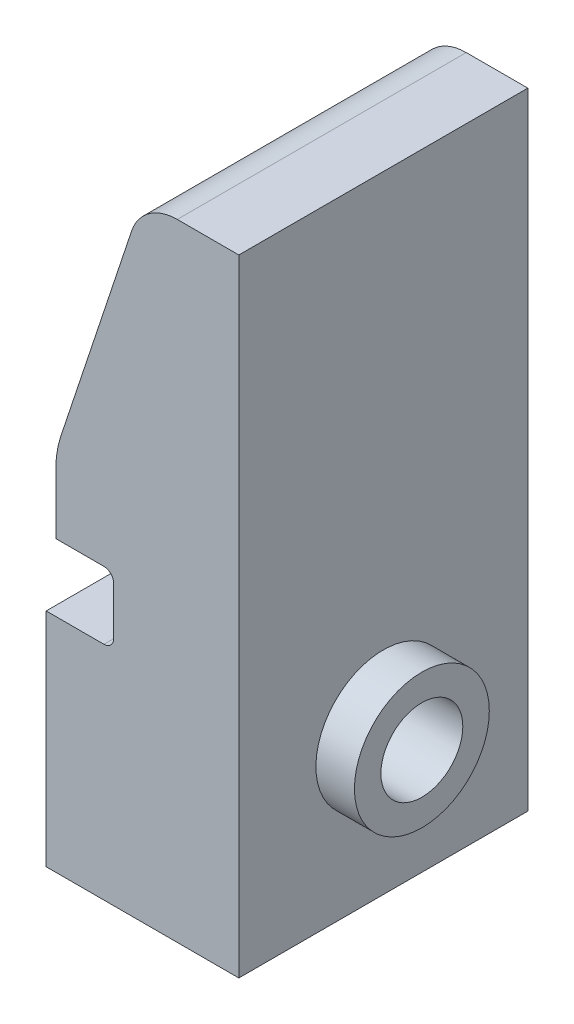
SolidWorks part; units mm, degrees
ref_plane "前视基准面" through (0, 0, 0) normal (0, 0, 1) x (1, 0, 0)
ref_plane "上视基准面" through (0, 0, 0) normal (0, 1, 0) x (1, 0, 0)
ref_plane "右视基准面" through (0, 0, 0) normal (1, 0, 0) x (0, 0, -1)
sketch "草图1" plane through (0, 0, 0) normal (0, 0, 1) x (1, 0, 0)
  line L0 (-4.332, 33.7247) -> (-13.332, 6.6194)
  line L1 (-4.332, 33.7247) -> (5.668, 33.7247)
  line L2 (-14.332, -1.2753) -> (-14.332, -31.2753)
  line L3 (-14.332, -31.2753) -> (5.668, -31.2753)
  line L4 (5.668, 33.7247) -> (5.668, -31.2753)
  line L5 (-14.332, -1.2753) -> (-13.332, -1.2753)
  line L6 (-13.332, -1.2753) -> (-13.332, 6.6194)
  dimension "D1" = 20
  dimension "D2" = 10
  dimension "D3" = 7.8947
  dimension "D4" = 30
  dimension "D5" = 1
  dimension "D6" = 65
extrude "凸台-拉伸1" add sketch "草图1" along normal blind 30
sketch "草图2" plane through (-14.332, 0, 0) normal (-1, 0, 0) x (0, 0, 1)
  line L0 (-8.9746, -16.2753) -> (37.5596, -16.2753) construction
  line L1 (15, 16.8661) -> (15, -37.0339) construction
  line L2 (0, -1.2753) -> (0, -31.2753) construction
  line L3 (30, -1.2753) -> (30, -31.2753) construction
  line L4 (30, -1.2753) -> (0, -1.2753) construction
  line L5 (30, -31.2753) -> (0, -31.2753) construction
  circle A0 centre (15, -16.2753) radius 4.25
  dimension "D1" = 8.5
extrude "切除-拉伸1" cut sketch "草图2" against normal blind 30 contours A0
fillet "圆角1" radius 10 1 edges at (-13.332, 6.6194, 15)
fillet "圆角2" radius 5 1 edges at (-4.332, 33.7247, 15)
sketch "草图5" plane through (0, 0, 30) normal (0, 0, 1) x (1, 0, 0)
  line L0 (-14.332, -1.2753) -> (-14.332, -31.2753) construction
  line L1 (-14.332, -1.2753) -> (-7.332, -1.2753)
  line L2 (-14.332, -1.2753) -> (-14.332, -8.2753)
  line L3 (-14.332, -8.2753) -> (-7.332, -8.2753)
  line L4 (-7.332, -1.2753) -> (-7.332, -8.2753)
  dimension "D1" = 7
  dimension "D2" = 7
extrude "切除-拉伸2" cut sketch "草图5" against normal blind 20
fillet "圆角5" radius 1 5 edges at (-7.332, -1.2753, 20) (-7.332, -8.2753, 20) (-10.832, -8.2753, 10) (-7.332, -4.7753, 10) (-10.332, -1.2753, 10)
sketch "草图6" plane through (5.668, 0, 0) normal (1, 0, 0) x (0, 0, -1)
  circle A0 centre (-15, -16.2753) radius 7
  circle A1 centre (-15, -16.2753) radius 4.25
  dimension "D1" = 14
extrude "凸台-拉伸2" add sketch "草图6" along normal blind 4
